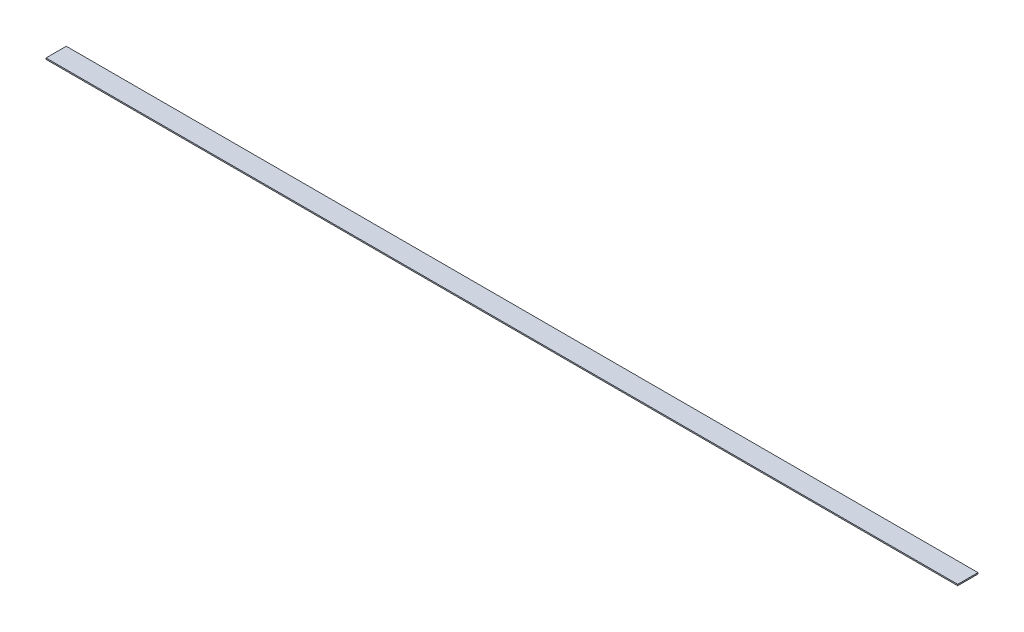
SolidWorks part; units mm, degrees
material "Very Low Density PE (SS)"
ref_plane "Front Plane" through (0, 0, 0) normal (0, 0, 1) x (1, 0, 0)
ref_plane "Top Plane" through (0, 0, 0) normal (0, 1, 0) x (1, 0, 0)
ref_plane "Right Plane" through (0, 0, 0) normal (1, 0, 0) x (0, 0, -1)
sketch "Sketch1" plane through (0, 0, 0) normal (0, 1, 0) x (1, 0, 0)
  line L1 (571.5, -12.7) -> (-571.5, -12.7)
  line L2 (571.5, -12.7) -> (571.5, 12.7)
  line L3 (571.5, 12.7) -> (-571.5, 12.7)
  line L4 (-571.5, -12.7) -> (-571.5, 12.7)
  line L5 (571.5, -12.7) -> (-571.5, 12.7) construction
  line L6 (571.5, 12.7) -> (-571.5, -12.7) construction
  point P0 (0, 0)
  dimension "D1" = 1143
  dimension "D2" = 25.4
extrude "Boss-Extrude1" add sketch "Sketch1" along normal blind 1.5875
